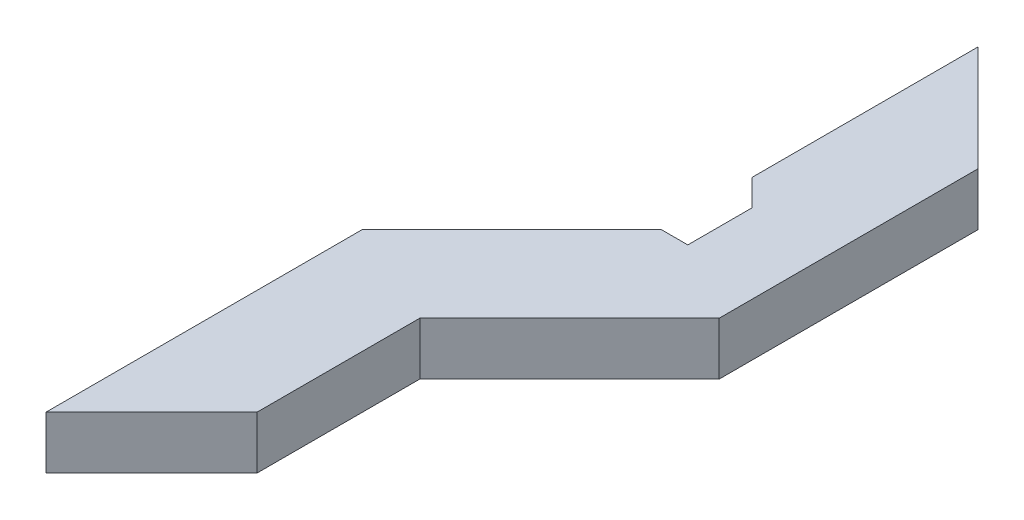
SolidWorks part; units mm, degrees
ref_plane "Front Plane" through (0, 0, 0) normal (0, 0, 1) x (1, 0, 0)
ref_plane "Top Plane" through (0, 0, 0) normal (0, 1, 0) x (1, 0, 0)
ref_plane "Right Plane" through (0, 0, 0) normal (1, 0, 0) x (0, 0, -1)
sketch "Sketch1" plane through (0, 0, 0) normal (0, 1, 0) x (1, 0, 0)
  line L0 (3.8971, -25.4312) -> (3.8971, 4.5688)
  line L1 (3.8971, 4.5688) -> (18.0392, 18.7109)
  line L2 (18.0843, 27.3163) -> (18.0843, 48.7109)
  line L3 (18.0843, 48.7109) -> (28.0843, 38.7109)
  line L4 (28.0843, 38.7109) -> (28.0843, 14.1872)
  line L5 (13.8971, 0) -> (28.0843, 14.1872)
  line L6 (3.8971, -25.4312) -> (13.8971, -15.4312)
  line L8 (18.0843, 27.3163) -> (20.5829, 24.7726)
  line L9 (20.5829, 24.7726) -> (20.5829, 18.7109)
  line L10 (18.0392, 18.7109) -> (20.5829, 18.7109)
  line L13 (13.8971, -15.4312) -> (13.8971, 0)
  dimension "D1" = 30
  dimension "D2" = 20
  dimension "D3" = 45
  dimension "D4" = 225
  dimension "D5" = 30
  dimension "D6" = 135
  dimension "D7" = 10
  dimension "D9" = 6.0617
extrude "Boss-Extrude1" add sketch "Sketch1" along normal blind 5
